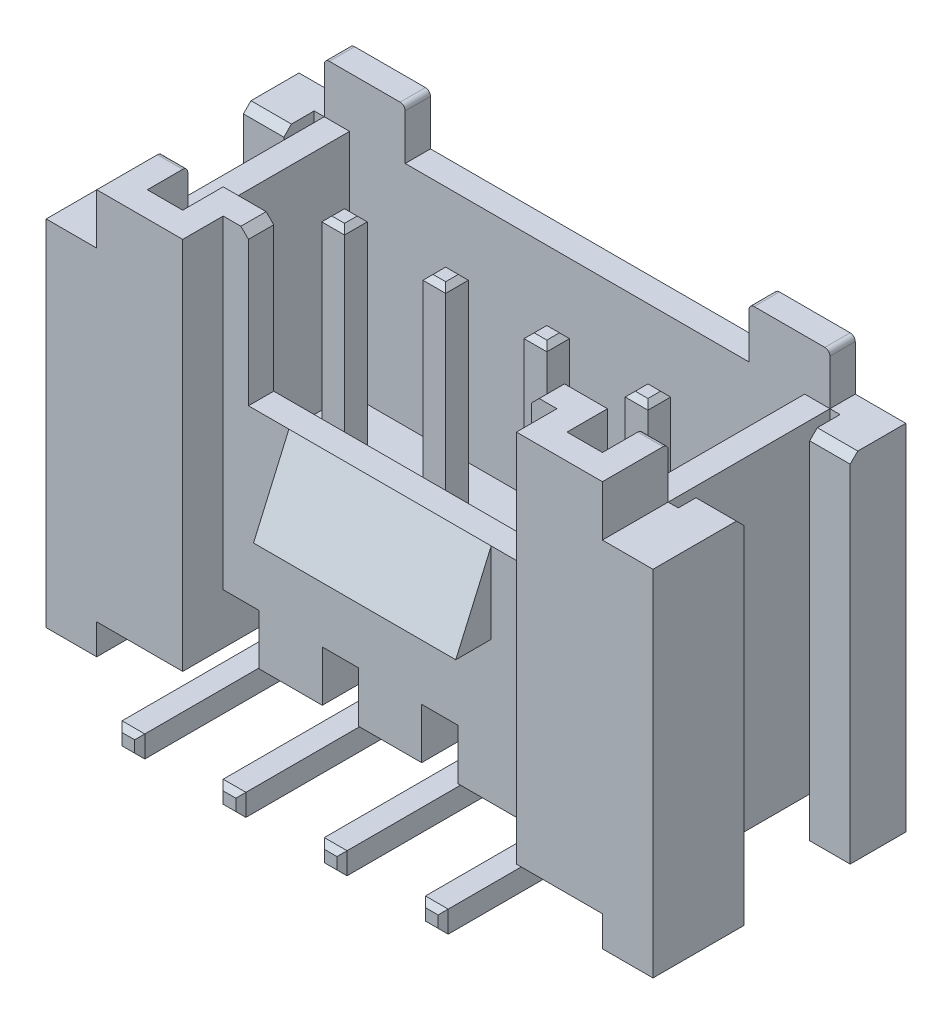
SolidWorks part; units mm, degrees
ref_plane "Plan de face" through (0, 0, 0) normal (0, 0, 1) x (1, 0, 0)
ref_plane "Plan de dessus" through (0, 0, 0) normal (0, 1, 0) x (1, 0, 0)
ref_plane "Plan de droite" through (0, 0, 0) normal (1, 0, 0) x (0, 0, -1)
sketch "Esquisse1" plane through (0, 0, 0) normal (0, 1, 0) x (1, 0, 0)
  line L1 (0, 0) -> (10, 0)
  line L2 (0, 0) -> (0, 5)
  line L3 (0, 5) -> (10, 5)
  line L4 (10, 0) -> (10, 5)
  dimension "D1" = 5
  dimension "D2" = 10
extrude "Boss.-Extru.1" add sketch "Esquisse1" along normal blind 7.4
sketch "Esquisse2" plane through (0, 7.4, 0) normal (0, 1, 0) x (1, 0, 0)
  line L0 (0, 0) -> (10, 0) construction
  line L1 (1.7, 0) -> (8.3, 0)
  line L2 (1.7, 0) -> (1.7, 0.8)
  line L3 (1.7, 0.8) -> (8.3, 0.8)
  line L4 (8.3, 0) -> (8.3, 0.8)
  line L5 (0, 5) -> (0, 0) construction
  line L6 (10, 0) -> (10, 5) construction
  dimension "D1" = 1.7
  dimension "D2" = 1.7
  dimension "D3" = 0.8
extrude "Enlèv. mat.-Extru.1" cut sketch "Esquisse2" against normal blind 8
sketch "Esquisse4" plane through (0, 7.4, 0) normal (0, 1, 0) x (1, 0, 0)
  line L16 (0.5, 0.5) -> (1.2, 0.5)
  line L17 (1.2, 0.5) -> (1.2, 1.3)
  line L18 (1.2, 1.3) -> (8.8, 1.3)
  line L19 (8.8, 1.3) -> (8.8, 0.5)
  line L20 (8.8, 0.5) -> (9.5, 0.5)
  line L21 (9.5, 0.5) -> (9.5, 4.5)
  line L22 (9.5, 4.5) -> (0.5, 4.5)
  line L23 (0.5, 4.5) -> (0.5, 0.5)
  line L24 (0.5, 0.5) -> (1.2, 0.5)
  line L25 (1.2, 0.5) -> (1.2, 1.3)
  line L26 (1.2, 1.3) -> (8.8, 1.3)
  line L27 (8.8, 1.3) -> (8.8, 0.5)
  line L28 (8.8, 0.5) -> (9.5, 0.5)
  line L29 (9.5, 0.5) -> (9.5, 4.5)
  line L30 (9.5, 4.5) -> (0.5, 4.5)
  line L31 (0.5, 4.5) -> (0.5, 0.5)
  dimension "D1" = 0.5
extrude "Enlèv. mat.-Extru.2" cut sketch "Esquisse4" against normal blind 5.5
sketch "Esquisse5" plane through (0, 7.4, 0) normal (0, 1, 0) x (1, 0, 0)
  line L0 (10, 5) -> (0, 5) construction
  line L1 (1.6, 5) -> (8.4, 5)
  line L2 (1.6, 5) -> (1.6, 4.5)
  line L3 (1.6, 4.5) -> (8.4, 4.5)
  line L4 (8.4, 5) -> (8.4, 4.5)
  line L5 (9.5, 4.5) -> (0.5, 4.5) construction
  line L6 (10, 0) -> (10, 5) construction
  line L7 (0, 5) -> (0, 0) construction
  line L8 (0.5, 4.5) -> (0.5, 0.5) construction
  line L9 (0, 4.5) -> (0.5, 4.5)
  line L10 (0, 4.5) -> (0, 1.3)
  line L11 (0, 1.3) -> (0.5, 1.3)
  line L12 (0.5, 4.5) -> (0.5, 1.3)
  line L13 (9.5, 0.5) -> (9.5, 4.5) construction
  line L14 (9.5, 4.5) -> (10, 4.5)
  line L15 (9.5, 4.5) -> (9.5, 1.3)
  line L16 (9.5, 1.3) -> (10, 1.3)
  line L17 (10, 4.5) -> (10, 1.3)
  line L18 (0, 0) -> (1.7, 0) construction
  line L19 (8.3, 0) -> (10, 0) construction
  dimension "D1" = 1.6
  dimension "D2" = 1.6
  dimension "D3" = 0.5
  dimension "D4" = 1.3
  dimension "D5" = 0.5
  dimension "D6" = 1.3
extrude "Enlèv. mat.-Extru.3" cut sketch "Esquisse5" against normal blind 1
sketch "Esquisse6" plane through (0, 7.4, 0) normal (0, 1, 0) x (1, 0, 0)
  line L0 (1.2, 1.3) -> (8.8, 1.3) construction
  line L1 (2.2, 1.3) -> (7.8, 1.3)
  line L2 (2.2, 1.3) -> (2.2, 0.8)
  line L3 (2.2, 0.8) -> (7.8, 0.8)
  line L4 (7.8, 1.3) -> (7.8, 0.8)
  line L5 (8.3, 0.8) -> (1.7, 0.8) construction
  line L6 (10, 0) -> (10, 1.3) construction
  line L7 (0, 5) -> (0, 4.5) construction
  dimension "D1" = 2.2
  dimension "D2" = 2.2
extrude "Enlèv. mat.-Extru.4" cut sketch "Esquisse6" against normal blind 3
sketch "Esquisse8" plane through (0, 0, 0) normal (0, -1, 0) x (1, 0, 0)
  line L0 (8.3, -0.8) -> (1.7, -0.8) construction
  line L1 (1.7, -0.8) -> (8.3, -0.8)
  line L2 (1.7, -0.8) -> (1.7, -5)
  line L3 (1.7, -5) -> (8.3, -5)
  line L4 (8.3, -0.8) -> (8.3, -5)
  line L5 (10, -5) -> (0, -5) construction
  line L6 (0, -5) -> (0, 0) construction
  line L7 (10, 0) -> (10, -5) construction
  dimension "D1" = 1.7
  dimension "D2" = 1.7
extrude "Enlèv. mat.-Extru.6" cut sketch "Esquisse8" against normal blind 1
sketch "Esquisse9" plane through (1.7, 0, 0) normal (1, 0, 0) x (0, 0, -1)
  line L0 (5, 1) -> (0.8, 1) construction
  line L1 (4.7, 1) -> (3.9, 0.2)
  line L2 (3.9, 0.2) -> (1.9, 0.2)
  line L3 (1.9, 0.2) -> (1.1, 1)
  line L4 (0, 0) -> (5, 0) construction
  line L5 (4.7, 1) -> (1.1, 1)
  dimension "D1" = 45
  dimension "D2" = 45
  dimension "D3" = 0.2
  dimension "D4" = 0.3
  dimension "D5" = 0.3
extrude "Boss.-Extru.2" add sketch "Esquisse9" along normal blind 6.8
ref_plane "Plan1" through (5, 0, 0) normal (1, 0, 0) x (0, 0, -1)
sketch "Esquisse11" plane through (5, 0, 0) normal (1, 0, 0) x (0, 0, -1)
  line L0 (0.8, 4.4) -> (0.1, 2.8)
  line L1 (0.1, 2.8) -> (0.8, 2.8)
  line L2 (0.8, 1) -> (0.8, 7.4) construction
  line L3 (0.8, 2.8) -> (0.8, 4.4)
  dimension "D1" = 1.6
  dimension "D2" = 0.7
extrude "Boss.-Extru.3" add sketch "Esquisse11" along normal blind 2 and the other way blind 2
ref_plane "Plan2" through (0, 1, 0) normal (0, 1, 0) x (1, 0, 0)
sketch "Esquisse17" plane through (0, 1, 0) normal (0, 1, 0) x (1, 0, 0)
  line L0 (3.035, 0.8) -> (3.035, 5) construction
  line L1 (5, 0.8) -> (5, 5) construction
  line L2 (6.965, 0.8) -> (6.965, 5) construction
  line L4 (1.7, 0.8) -> (1.7, 5) construction
  line L8 (2.41, 0.8) -> (3.66, 0.8)
  line L9 (3.66, 0.8) -> (3.66, 5)
  line L10 (3.66, 5) -> (2.41, 5)
  line L11 (2.41, 5) -> (2.41, 0.8)
  line L16 (4.375, 0.8) -> (5.625, 0.8)
  line L17 (5.625, 0.8) -> (5.625, 5)
  line L18 (5.625, 5) -> (4.375, 5)
  line L19 (4.375, 5) -> (4.375, 0.8)
  line L24 (6.34, 0.8) -> (7.59, 0.8)
  line L25 (7.59, 0.8) -> (7.59, 5)
  line L26 (7.59, 5) -> (6.34, 5)
  line L27 (6.34, 5) -> (6.34, 0.8)
  dimension "D1" = 1.25
  dimension "D2" = 1.25
  dimension "D3" = 1.25
  dimension "D4" = 3.3
  dimension "D5" = 1.34
  dimension "D6" = 1.34
extrude "Boss.-Extru.8" add sketch "Esquisse17" against normal blind 1
chamfer "Chanfrein1" distance 0.15 angle 45 2 edges at (2.2, 7.4, -1.05) (7.8, 7.4, -1.05)
sketch "Esquisse13" plane through (0, 0.2, 0) normal (0, -1, 0) x (1, 0, 0)
  line L0 (5, -0.8) -> (5, -4.7975) construction
  line L1 (3.775, -2.9) -> (2.225, -2.9) construction
  line L2 (4.375, -1.9) -> (3.66, -1.9) construction
  line L3 (8.225, -3.125) -> (8.225, -2.675)
  line L4 (4.225, -3.125) -> (3.775, -3.125)
  line L5 (3, -0.8) -> (7, -0.8) construction
  line L6 (4.225, -3.125) -> (4.225, -2.675)
  line L7 (4.225, -2.675) -> (3.775, -2.675)
  line L8 (3.775, -3.125) -> (3.775, -2.675)
  line L9 (2.225, -3.125) -> (1.775, -3.125)
  line L11 (2.41, -0.8) -> (3.66, -0.8) construction
  line L12 (2.225, -3.125) -> (2.225, -2.675)
  line L13 (2.225, -2.675) -> (1.775, -2.675)
  line L14 (1.775, -3.125) -> (1.775, -2.675)
  line L16 (7.775, -3.125) -> (8.225, -3.125)
  line L17 (7.775, -3.125) -> (7.775, -2.675)
  line L18 (7.775, -2.675) -> (8.225, -2.675)
  line L19 (6.225, -3.125) -> (6.225, -2.675)
  line L20 (5.775, -2.675) -> (6.225, -2.675)
  line L21 (5.775, -3.125) -> (5.775, -2.675)
  line L22 (5.775, -3.125) -> (6.225, -3.125)
  point P14 (3.035, -0.8)
  dimension "D1" = 1
  dimension "D2" = 0.45
  dimension "D3" = 2
  dimension "D4" = 2
extrude "Boss.-Extru.5" add sketch "Esquisse13" along normal blind 0.8 and the other way blind 6.3
fillet "Congé2" radius 0.1 6 edges at (0.25, 7.4, -1.3) (0, 7.4, -4.75) (1.6, 7.4, -4.75) (8.4, 7.4, -4.75) (10, 7.4, -4.75) (9.75, 7.4, -1.3)
sketch "Esquisse14" plane through (0, 0, -3.125) normal (0, 0, -1) x (-1, 0, 0)
  line L1 (-7.775, 0.2) -> (-7.775, -0.6) construction
  line L2 (-8.225, -0.6) -> (-7.775, -0.6)
  line L3 (-8.225, -0.6) -> (-8.225, -0.17)
  line L4 (-8.225, -0.17) -> (-7.775, -0.17)
  line L5 (-7.775, -0.6) -> (-7.775, -0.17)
  line L7 (-6.225, -0.6) -> (-5.775, -0.6)
  line L8 (-6.225, -0.6) -> (-6.225, -0.17)
  line L9 (-6.225, -0.17) -> (-5.775, -0.17)
  line L10 (-5.775, -0.6) -> (-5.775, -0.17)
  line L11 (-4.225, -0.6) -> (-3.775, -0.6)
  line L12 (-4.225, -0.6) -> (-4.225, -0.17)
  line L13 (-4.225, -0.17) -> (-3.775, -0.17)
  line L14 (-3.775, -0.6) -> (-3.775, -0.17)
  line L15 (-2.225, -0.6) -> (-1.775, -0.6)
  line L16 (-2.225, -0.6) -> (-2.225, -0.17)
  line L17 (-2.225, -0.17) -> (-1.775, -0.17)
  line L18 (-1.775, -0.6) -> (-1.775, -0.17)
  dimension "D1" = 0.43
  dimension "D2" = 4
extrude "Boss.-Extru.6" add sketch "Esquisse14" against normal blind 4.5
chamfer "Chanfrein2" distance 0.1 angle 45 32 edges at (5.775, 6.5, -2.9) (2, 6.5, -2.675) (1.775, 6.5, -2.9) (2, 6.5, -3.125) (2.225, 6.5, -2.9) (4, 6.5, -2.675) (3.775, 6.5, -2.9) (4, 6.5, -3.125) (4.225, 6.5, -2.9) (6.225, 6.5, -2.9) (6, 6.5, -2.675) (6, 6.5, -3.125) (8.225, 6.5, -2.9) (8, 6.5, -2.675) (7.775, 6.5, -2.9) (8, 6.5, -3.125) (2, -0.6, 1.375) (1.775, -0.385, 1.375) (2, -0.17, 1.375) (2.225, -0.385, 1.375) (4, -0.6, 1.375) (3.775, -0.385, 1.375) (4, -0.17, 1.375) (4.225, -0.385, 1.375) (6, -0.6, 1.375) (5.775, -0.385, 1.375) (6, -0.17, 1.375) (6.225, -0.385, 1.375) (8, -0.6, 1.375) (7.775, -0.385, 1.375) (8, -0.17, 1.375) (8.225, -0.385, 1.375)
sketch "Esquisse16" plane through (0, 6.4, 0) normal (0, 1, 0) x (1, 0, 0)
  line L0 (0, 5) -> (-1, 5) construction
  line L1 (-1, 5) -> (-1, 0) construction
  line L2 (-1, 0) -> (0, 0) construction
  line L3 (0, 1.2) -> (0, 0) construction
  line L5 (0, 4.5) -> (-0.2, 4.5)
  line L6 (0, 4.5) -> (0, 5)
  line L7 (0, 5) -> (-0.2, 5)
  line L8 (0, 0) -> (-1, 0)
  line L9 (-1, 5) -> (-0.2, 5)
  line L10 (-1, 5) -> (-1, 3.9)
  line L11 (-1, 3.9) -> (-0.2, 3.9)
  line L12 (-0.2, 4.5) -> (-0.2, 3.9)
  line L13 (0, 0) -> (0, 1.3)
  line L14 (0, 1.3) -> (-0.2, 1.3)
  line L15 (-1, 0) -> (-1, 1.3)
  line L16 (0, 1.3) -> (0.5, 1.3) construction
  line L17 (-1, 1.3) -> (-1, 1.8)
  line L18 (-1, 1.8) -> (-0.2, 1.8)
  line L19 (-0.2, 1.3) -> (-0.2, 1.8)
  line L20 (5, 5) -> (5, 0.8) construction
  line L21 (8.4, 5) -> (1.6, 5) construction
  line L22 (3, 0.8) -> (7, 0.8) construction
  line L23 (10.2, 4.5) -> (10.2, 3.9)
  line L24 (11, 1.3) -> (11, 1.8)
  line L25 (11, 0) -> (11, 1.3)
  line L26 (10, 0) -> (11, 0)
  line L27 (10, 0) -> (10, 1.3)
  line L28 (10, 1.3) -> (10.2, 1.3)
  line L29 (10.2, 1.3) -> (10.2, 1.8)
  line L30 (11, 1.8) -> (10.2, 1.8)
  line L31 (10, 4.5) -> (10.2, 4.5)
  line L32 (10, 4.5) -> (10, 5)
  line L33 (10, 5) -> (10.2, 5)
  line L34 (11, 5) -> (10.2, 5)
  line L35 (11, 5) -> (11, 3.9)
  line L36 (11, 3.9) -> (10.2, 3.9)
  line L37 (0, 5) -> (0, 4.5)
  line L38 (0, 1.3) -> (0, 0)
  line L39 (10, 1.3) -> (10, 0)
  line L40 (10, 4.5) -> (10, 5)
  dimension "D1" = 1
  dimension "D2" = 0.8
  dimension "D3" = 1.1
  dimension "D4" = 0.8
  dimension "D5" = 1.8
  dimension "D6" = 0
extrude "Boss.-Extru.7" add sketch "Esquisse16" against normal blind 7 contours L14 L19 L18 L17 L15 L8 L13 | L12 L5 L6 L7 L9 L10 L11 | L36 L35 L34 L33 L32 L31 L23 | L24 L30 L29 L28 L27 L26 L25
chamfer "Chanfrein4" distance 0.15 angle 45 4 edges at (10.6, 6.4, -3.9) (10.6, 6.4, -1.8) (-0.6, 6.4, -1.8) (-0.6, 6.4, -3.9)
fillet "Congé3" radius 0.1 8 edges at (2, -0.6, -3.125) (2, -0.17, -2.675) (4, -0.6, -3.125) (4, -0.17, -2.675) (6, -0.6, -3.125) (6, -0.17, -2.675) (8, -0.6, -3.125) (8, -0.17, -2.675)
